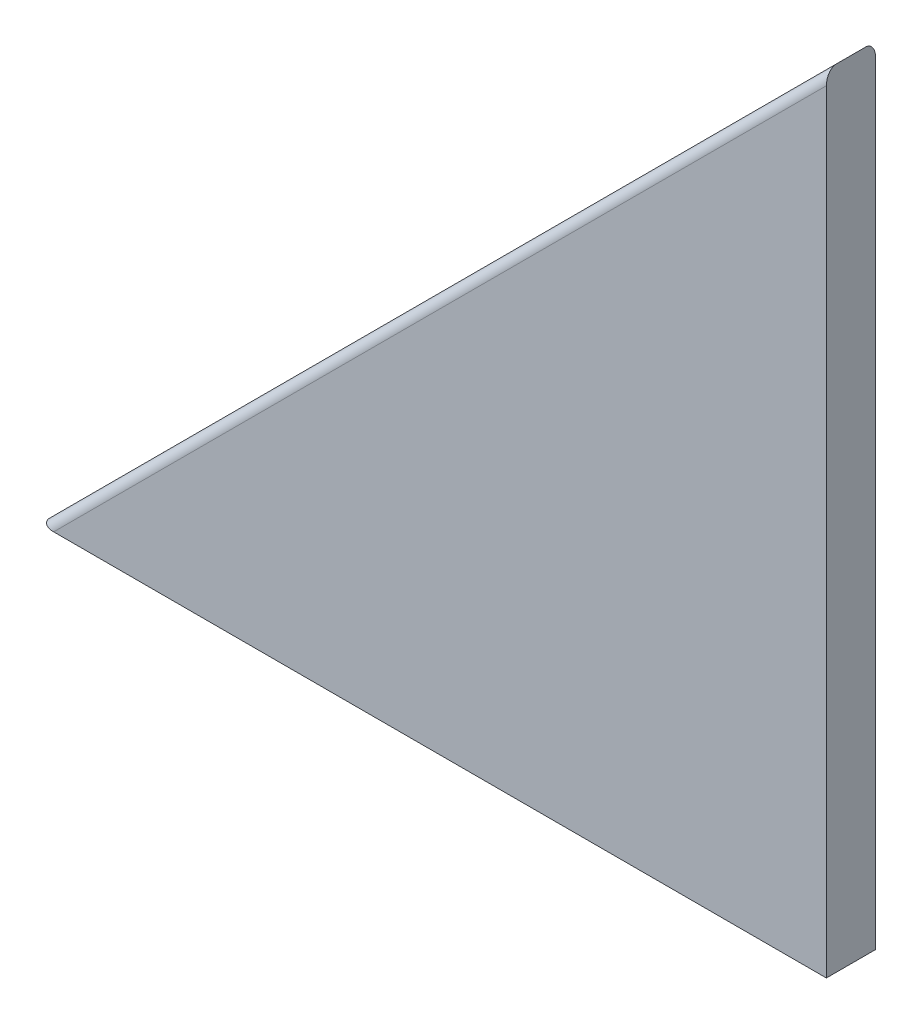
SolidWorks part; units mm, degrees
material "ASTM A36 Steel"
ref_plane "Front Plane" through (0, 0, 0) normal (0, 0, 1) x (1, 0, 0)
ref_plane "Top Plane" through (0, 0, 0) normal (0, 1, 0) x (1, 0, 0)
ref_plane "Right Plane" through (0, 0, 0) normal (1, 0, 0) x (0, 0, -1)
sketch "Sketch1" plane through (0, 0, 0) normal (0, 0, 1) x (1, 0, 0)
  line L0 (0, 0) -> (-101.6, 0)
  line L1 (-101.6, 0) -> (0, 101.6)
  line L2 (0, 101.6) -> (0, 0)
  dimension "D1" = 101.6
  dimension "D2" = 101.6
extrude "Boss-Extrude1" add sketch "Sketch1" along normal blind 6.35
fillet "Fillet2" radius 1.27 1 edges at (-50.8, 50.8, 6.35)
fillet "Fillet3" radius 1.27 1 edges at (-50.8, 50.8, 0)
